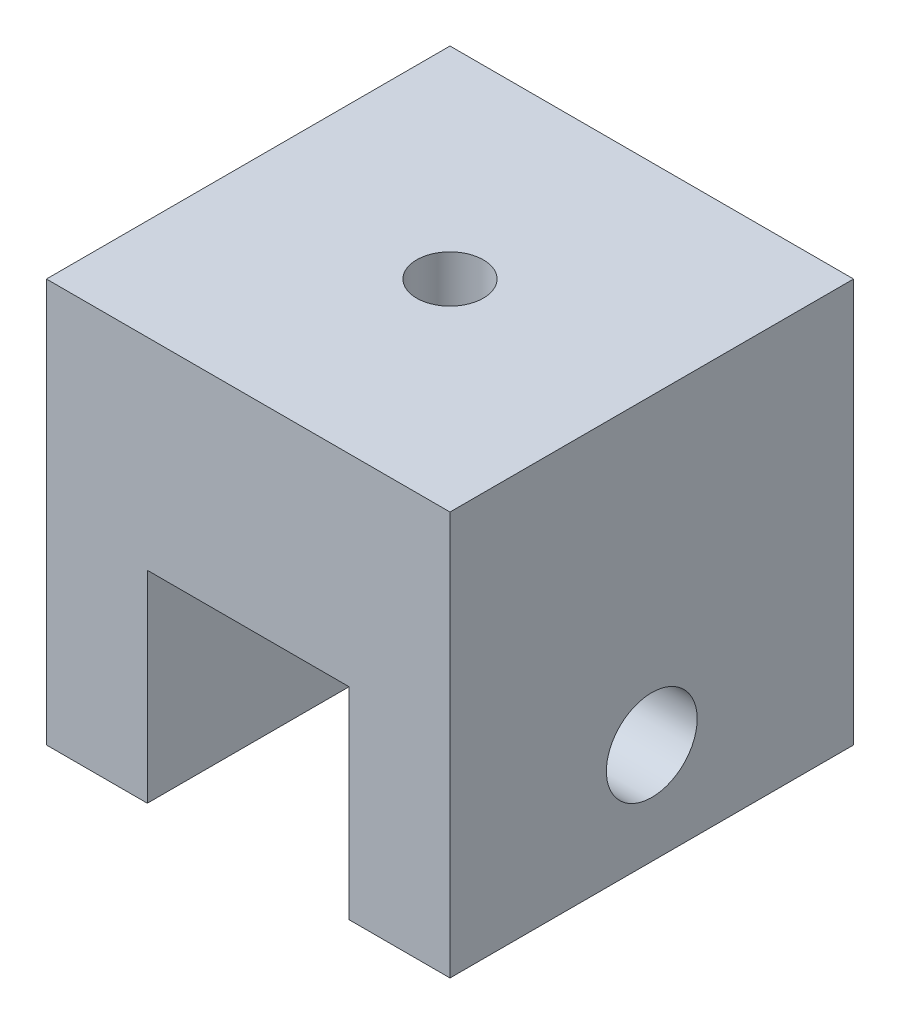
SolidWorks part; units mm, degrees
ref_plane "Front Plane" through (0, 0, 0) normal (0, 0, 1) x (1, 0, 0)
ref_plane "Top Plane" through (0, 0, 0) normal (0, 1, 0) x (1, 0, 0)
ref_plane "Right Plane" through (0, 0, 0) normal (1, 0, 0) x (0, 0, -1)
sketch "Sketch1" plane through (0, 0, 0) normal (0, 1, 0) x (1, 0, 0)
  line L1 (-20, -20) -> (20, -20)
  line L2 (-20, -20) -> (-20, 20)
  line L3 (-20, 20) -> (20, 20)
  line L4 (20, -20) -> (20, 20)
  line L5 (-20, -20) -> (20, 20) construction
  line L6 (-20, 20) -> (20, -20) construction
  point P0 (0, 0)
  dimension "D1" = 40
  dimension "D2" = 40
extrude "Boss-Extrude1" add sketch "Sketch1" along normal blind 40
sketch "Sketch2" plane through (0, 40, 0) normal (0, 1, 0) x (1, 0, 0)
  circle A0 centre (0, 0) radius 3.3
  dimension "D1" = 6.6
extrude "Cut-Extrude1" cut sketch "Sketch2" against normal blind 40
sketch "Sketch3" plane through (0, 0, 20) normal (0, 0, 1) x (1, 0, 0)
  line L1 (-10, -20) -> (10, -20)
  line L2 (-10, -20) -> (-10, 20)
  line L3 (-10, 20) -> (10, 20)
  line L4 (10, -20) -> (10, 20)
  line L5 (-10, -20) -> (10, 20) construction
  line L6 (-10, 20) -> (10, -20) construction
  point P0 (0, 0)
  dimension "D1" = 20
  dimension "D2" = 40
extrude "Cut-Extrude2" cut sketch "Sketch3" against normal blind 40
sketch "Sketch4" plane through (20, 0, 0) normal (1, 0, 0) x (0, 0, -1)
  line L0 (-20, 0) -> (20, 0) construction
  circle A0 centre (0, 10) radius 4.5
  point P4 (0, 0)
  dimension "D1" = 9
  dimension "D2" = 10
extrude "Cut-Extrude3" cut sketch "Sketch4" against normal blind 40
